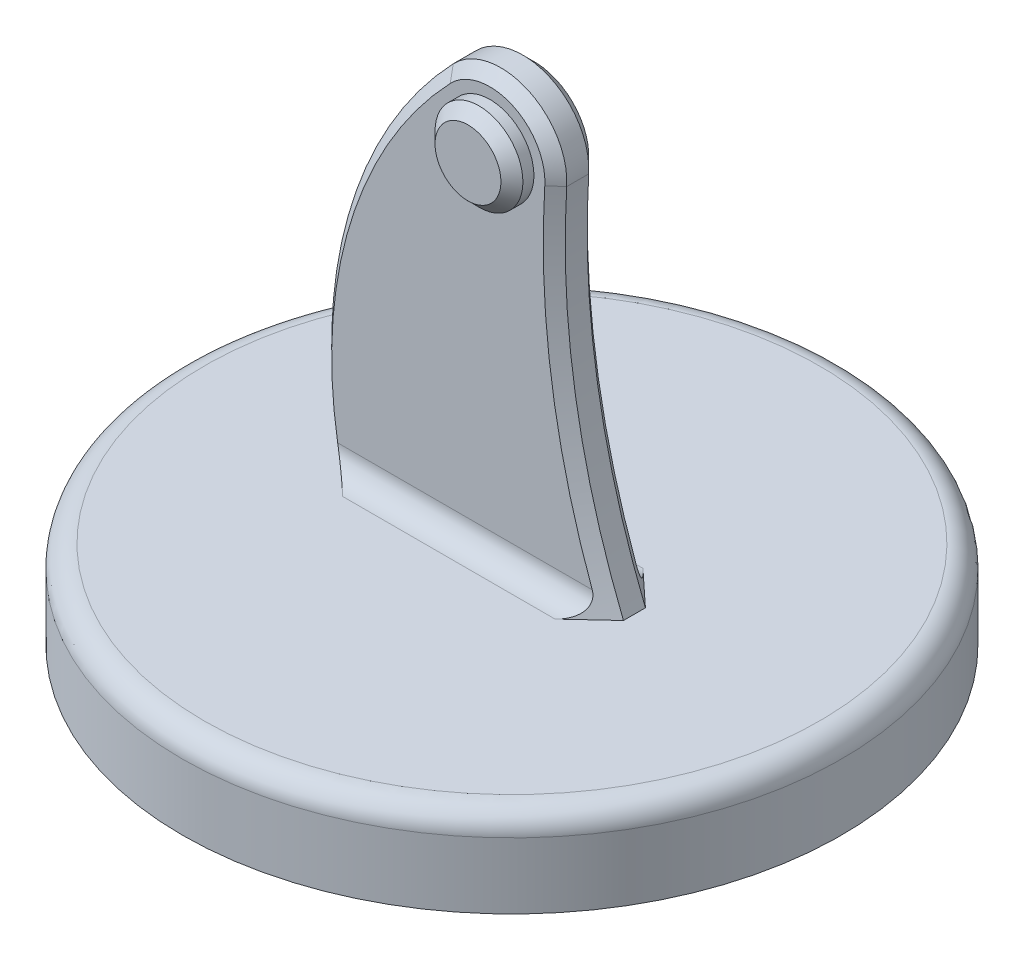
SolidWorks part; units mm, degrees
ref_plane "Front Plane" through (0, 0, 0) normal (0, 0, 1) x (1, 0, 0)
ref_plane "Top Plane" through (0, 0, 0) normal (0, 1, 0) x (1, 0, 0)
ref_plane "Right Plane" through (0, 0, 0) normal (1, 0, 0) x (0, 0, -1)
sketch "Sketch1" plane through (0, 0, 0) normal (0, 1, 0) x (1, 0, 0)
  circle A0 centre (0, 0) radius 75
  dimension "D1" = 150
extrude "Boss-Extrude1" add sketch "Sketch1" along normal blind 20
fillet "Fillet1" radius 5 1 edges at (0, 20, 75)
sketch "Sketch2" plane through (0, 0, 0) normal (0, 0, 1) x (1, 0, 0)
  line L0 (0, 0) -> (0, 100) construction
  line L2 (0, 15) -> (30, 15) construction
  line L3 (-75, 15) -> (75, 15) construction
  line L4 (0, 15) -> (-35, 15) construction
  line L5 (-35, 15) -> (30, 15)
  arc A0 (14.9706, 99.062) -> (-10.8492, 110.3583) centre (0, 100) ccw
  arc A1 (30, 15) -> (14.9706, 99.062) centre (194.6184, 87.8065) cw
  arc A2 (-35, 15) -> (-10.8492, 110.3583) centre (61.4788, 41.3028) cw
  dimension "D4" = 30
  dimension "D5" = 180
  dimension "D6" = 100
  dimension "D1" = 30
  dimension "D2" = 35
  dimension "D3" = 100
extrude "Boss-Extrude2" add sketch "Sketch2" along normal mid plane 10
chamfer "Chamfer1" distance 2.5 angle 45 6 edges at (-34.7965, 68.3412, -5) (6.0123, 113.7423, -5) (16.9703, 58.8038, -5) (-34.7965, 68.3412, 5) (6.0123, 113.7423, 5) (16.9703, 58.8038, 5)
fillet "Fillet2" radius 5 2 edges at (-4.2415, 20, -5) (-4.2415, 20, 5)
sketch "Sketch3" plane through (0, 0, 5) normal (0, 0, 1) x (1, 0, 0)
  circle A0 centre (0, 100) radius 10
  dimension "D1" = 20
extrude "Boss-Extrude3" add sketch "Sketch3" along normal blind 5
chamfer "Chamfer2" distance 2.5 angle 45 1 edges at (10, 100, 10)
sketch "Sketch4" plane through (0, 0, -5) normal (0, 0, -1) x (-1, 0, 0)
  circle A0 centre (0, 100) radius 5
  dimension "D1" = 10
extrude "Cut-Extrude1" cut sketch "Sketch4" against normal blind 10
